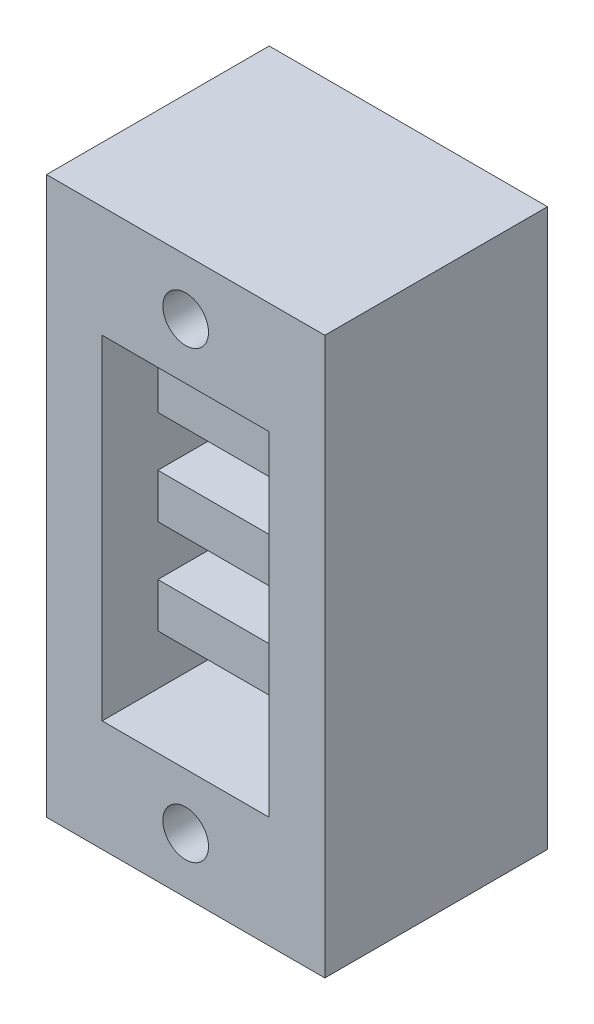
SolidWorks part; units mm, degrees
ref_plane "Front Plane" through (0, 0, 0) normal (0, 0, 1) x (1, 0, 0)
ref_plane "Top Plane" through (0, 0, 0) normal (0, 1, 0) x (1, 0, 0)
ref_plane "Right Plane" through (0, 0, 0) normal (1, 0, 0) x (0, 0, -1)
sketch "Sketch1" plane through (0, 0, 0) normal (0, 1, 0) x (1, 0, 0)
  line L1 (-6.35, -5.08) -> (6.35, -5.08)
  line L2 (-6.35, -5.08) -> (-6.35, 5.08)
  line L3 (-6.35, 5.08) -> (6.35, 5.08)
  line L4 (6.35, -5.08) -> (6.35, 5.08)
  line L5 (-6.35, -5.08) -> (6.35, 5.08) construction
  line L6 (-6.35, 5.08) -> (6.35, -5.08) construction
  point P0 (0, 0)
  dimension "D1" = 12.7
  dimension "D2" = 10.16
extrude "Boss-Extrude1" add sketch "Sketch1" along normal blind 25.4
sketch "Sketch2" plane through (0, 0, 5.08) normal (0, 0, 1) x (1, 0, 0)
  line L0 (-6.35, 25.4) -> (-6.35, 0) construction
  line L1 (-3.81, 5.08) -> (3.81, 5.08)
  line L2 (-3.81, 5.08) -> (-3.81, 20.32)
  line L3 (-3.81, 20.32) -> (3.81, 20.32)
  line L4 (3.81, 5.08) -> (3.81, 20.32)
  line L5 (6.35, 25.4) -> (6.35, 0) construction
  line L6 (-6.35, 25.4) -> (6.35, 25.4) construction
  line L8 (-6.35, 0) -> (6.35, 0) construction
  line L11 (6.35, 0) -> (6.35, 25.4) construction
  dimension "D1" = 2.54
  dimension "D2" = 2.54
  dimension "D4" = 5.08
  dimension "D3" = 5.08
extrude "Cut-Extrude1" cut sketch "Sketch2" against normal offset from surface (7.62 mm away) 2.54 up to face at (0, 12.7, -5.08)
sketch "Sketch3" plane through (3.81, 0, 0) normal (-1, 0, 0) x (0, 0, 1)
  line L0 (-2.54, 20.32) -> (-2.54, 5.08) construction
  line L1 (-2.54, 13.716) -> (2.54, 13.716)
  line L2 (-2.54, 13.716) -> (-2.54, 11.684)
  line L3 (-2.54, 11.684) -> (2.54, 11.684)
  line L4 (2.54, 13.716) -> (2.54, 11.684)
  line L5 (-2.54, 12.7) -> (5.08, 12.7) construction
  line L6 (-2.54, 9.398) -> (2.54, 9.398)
  line L7 (-2.54, 9.398) -> (-2.54, 7.366)
  line L8 (-2.54, 7.366) -> (2.54, 7.366)
  line L9 (2.54, 9.398) -> (2.54, 7.366)
  line L10 (-2.54, 16.002) -> (2.54, 16.002)
  line L11 (-2.54, 16.002) -> (-2.54, 18.034)
  line L12 (-2.54, 18.034) -> (2.54, 18.034)
  line L13 (2.54, 16.002) -> (2.54, 18.034)
  line L14 (5.08, 5.08) -> (5.08, 20.32) construction
  point P14 (0, 9.398)
  point P21 (5.08, 12.7)
  dimension "D1" = 2.286
  dimension "D2" = 2.286
  dimension "D3" = 2.032
  dimension "D4" = 2.032
  dimension "D5" = 2.032
  dimension "D6" = 5.08
  dimension "D7" = 5.08
  dimension "D8" = 5.08
extrude "Boss-Extrude2" add sketch "Sketch3" along normal up to surface (7.62 mm away) up to face at (-3.81, 12.7, 1.27)
sketch "Sketch4" plane through (0, 0, -2.54) normal (0, 0, 1) x (1, 0, 0)
  line L1 (-3.81, 7.366) -> (3.81, 7.366)
  line L2 (-3.81, 7.366) -> (-3.81, 5.08)
  line L3 (-3.81, 5.08) -> (3.81, 5.08)
  line L4 (3.81, 7.366) -> (3.81, 5.08)
extrude "Cut-Extrude2" cut sketch "Sketch4" against normal through all
sketch "Sketch5" plane through (0, 0, 5.08) normal (0, 0, 1) x (1, 0, 0)
  line L0 (0, 25.4) -> (0, 20.32) construction
  line L3 (0, 5.08) -> (0, 0) construction
  line L4 (-3.81, 5.08) -> (3.81, 5.08) construction
  line L5 (-6.35, 25.4) -> (6.35, 25.4) construction
  line L6 (-3.81, 20.32) -> (3.81, 20.32) construction
  circle A1 centre (0, 2.54) radius 1.0414
  circle A2 centre (0, 22.86) radius 1.0414
extrude "Cut-Extrude4" cut sketch "Sketch5" against normal through all
equation "\"D2@Sketch2\"=\"D1@Sketch2\""
equation "\"D2@Sketch3\"=\"D1@Sketch3\""
equation "\"D4@Sketch3\"=\"D3@Sketch3\""
equation "\"D5@Sketch3\"=\"D4@Sketch3\""
equation "\"D7@Sketch3\"=\"D6@Sketch3\""
equation "\"D8@Sketch3\"=\"D6@Sketch3\""
equation "\"D3@Sketch2\"=\"D4@Sketch2\""
